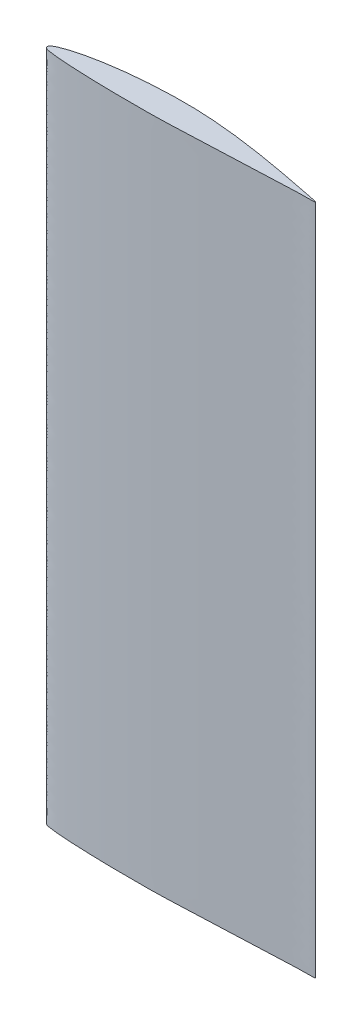
SolidWorks part; units mm, degrees
ref_plane "Front Plane" through (0, 0, 0) normal (0, 0, 1) x (1, 0, 0)
ref_plane "Top Plane" through (0, 0, 0) normal (0, 1, 0) x (1, 0, 0)
ref_plane "Right Plane" through (0, 0, 0) normal (1, 0, 0) x (0, 0, -1)
sketch "Sketch1" plane through (0, 0, 0) normal (0, 1, 0) x (1, 0, 0)
  spline S0 degree 3 poles (94.1981, -0.1347) (102.8862, -0.2593) (94.2687, 1.1836) (90.2783, 2.0832) (85.0415, 3.0799) (80.1264, 3.9828) (75.112, 4.8326) (70.1111, 5.5996) (65.094, 6.2726) (60.0708, 6.8435) (55.0396, 7.2899) (50.0026, 7.6002) (44.9607, 7.7259) (39.918, 7.6981) (34.876, 7.519) (29.8353, 7.2101) (24.7966, 6.7624) (19.7625, 6.1535) (14.7311, 5.3761) (9.7067, 4.364) (5.5292, 3.274) (2.6572, 2.2093) (1.2639, 1.5762) (0.6351, 1.1497) (0.1808, 0.7581) (-0.2514, -0.0537) (0.4728, -0.5637) (1.0019, -0.7738) (1.6945, -0.9544) (3.1376, -1.1529) (5.2446, -1.3855) (7.7591, -1.5785) (11.0917, -1.7952) (15.2472, -1.9832) (20.2249, -2.1568) (25.1946, -2.2688) (31.8122, -2.3568) (38.4273, -2.3547) (46.6976, -2.2159) (53.3119, -1.883) (59.9356, -1.6252) (64.9118, -1.4213) (69.8978, -1.2201) (74.8865, -1.017) (79.9087, -0.8161) (84.8535, -0.6066) (90.1378, -0.4265) (94.1981, -0.1347) (102.8862, -0.2593) (94.2687, 1.1836) knots -0.074591 -0.049762 -0.024883 0 0.025099 0.05011 0.075131 0.100155 0.125174 0.15018 0.175165 0.200127 0.225062 0.249971 0.274861 0.29975 0.324652 0.349579 0.374544 0.399567 0.424676 0.44993 0.47547 0.488518 0.495251 0.498115 0.499656 0.504317 0.50882 0.510253 0.512929 0.519317 0.531865 0.544298 0.556674 0.581328 0.605909 0.630447 0.654956 0.703935 0.728423 0.777462 0.802017 0.826606 0.851234 0.875909 0.900633 0.925409 0.950238 0.975117 1 1.025099 1.05011 1.075131 only from (100, 0) to (100, 0)
  point P0 (0, 0)
  point P1 (0.3409, 0.8804)
  point P3 (0.5722, 1.0899)
  point P4 (1.0498, 1.4192)
  point P5 (2.2729, 2.0225)
  point P6 (4.7467, 2.9522)
  point P7 (9.7352, 4.3209)
  point P8 (14.7476, 5.3398)
  point P9 (19.7719, 6.1267)
  point P10 (24.8033, 6.7362)
  point P11 (29.8396, 7.1873)
  point P12 (34.8788, 7.4975)
  point P13 (44.9604, 7.7003)
  point P14 (39.9194, 7.6729)
  point P15 (50, 7.5695)
  point P16 (55.0361, 7.2674)
  point P17 (60.0668, 6.823)
  point P18 (65.0906, 6.2559)
  point P19 (70.1064, 5.5842)
  point P20 (75.1129, 4.819)
  point P21 (80.1094, 3.974)
  point P22 (85.0954, 3.0642)
  point P23 (90.0705, 2.0994)
  point P24 (95.0356, 1.0939)
  point P25 (0, 0)
  point P26 (100, 0)
  point P27 (0.6591, -0.6304)
  point P28 (0.9278, -0.7399)
  point P29 (1.4502, -0.8842)
  point P30 (2.7271, -1.0925)
  point P31 (5.2533, -1.3722)
  point P32 (7.7633, -1.5739)
  point P33 (10.2648, -1.7359)
  point P34 (15.2524, -1.9748)
  point P35 (20.2281, -2.1467)
  point P36 (25.1967, -2.2612)
  point P37 (30.1604, -2.3273)
  point P38 (40.0806, -2.3179)
  point P39 (45.0396, -2.2253)
  point P40 (50, -2.0545)
  point P41 (54.9639, -1.825)
  point P42 (59.9332, -1.6236)
  point P43 (64.9094, -1.4219)
  point P44 (69.8936, -1.22)
  point P45 (74.8871, -1.0176)
  point P46 (79.8906, -0.8149)
  point P47 (89.9295, -0.4081)
  point P48 (94.9644, -0.2041)
  point P49 (84.9046, -0.6117)
extrude "Boss-Extrude1" add sketch "Sketch1" along normal blind 250
